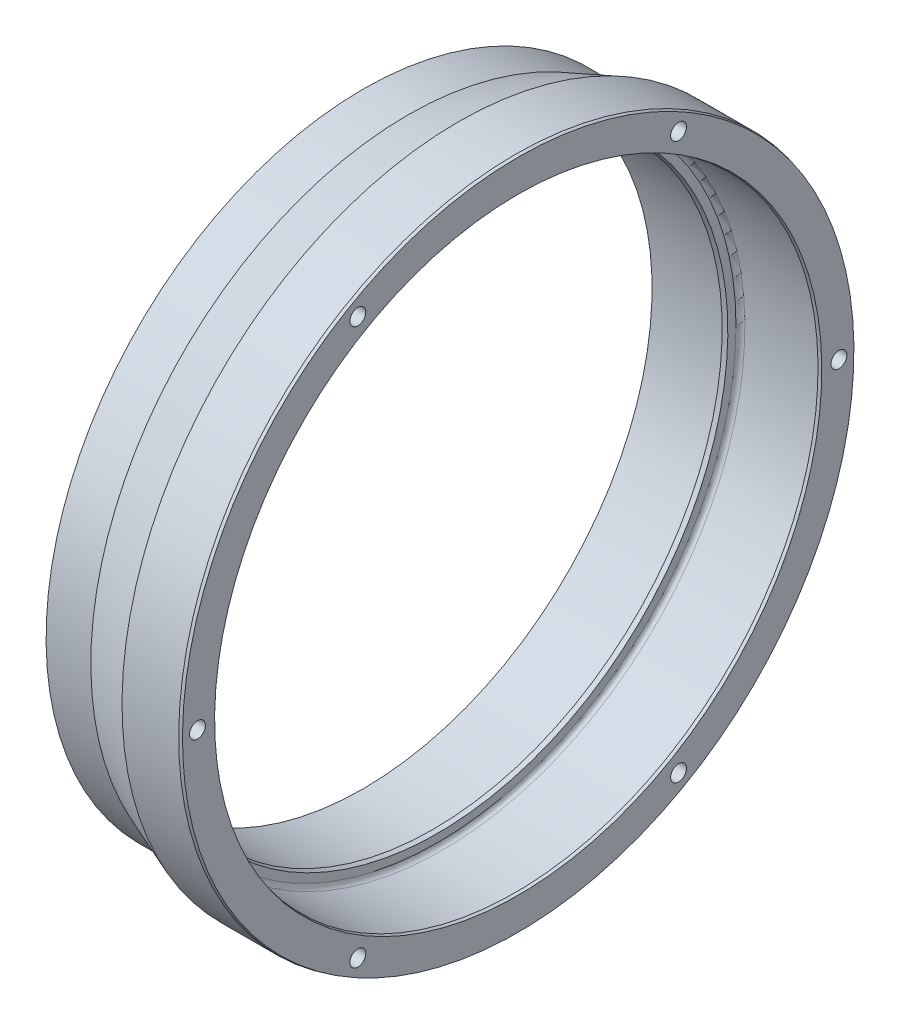
SolidWorks part; units mm, degrees
ref_plane "Front Plane" through (0, 0, 0) normal (0, 0, 1) x (1, 0, 0)
ref_plane "Top Plane" through (0, 0, 0) normal (0, 1, 0) x (1, 0, 0)
ref_plane "Right Plane" through (0, 0, 0) normal (1, 0, 0) x (0, 0, -1)
sketch "Sketch1" plane through (0, 0, 0) normal (0, 0, 1) x (1, 0, 0)
  line L0 (-18.796, 53.975) -> (-10.16, 57.3024)
  line L2 (0, 0) -> (0, 59.8495) construction
  line L3 (-0.508, 57.3024) -> (-10.16, 57.3024)
  line L5 (-18.796, 53.975) -> (-26.416, 53.975)
  line L7 (0, 0) -> (-26.416, 0) construction
  line L8 (-26.416, 53.975) -> (-26.416, 0) construction
  line L9 (-14.478, 49.2125) -> (-13.716, 49.4167)
  line L11 (0, 0) -> (0, 54.3464) construction
  line L12 (-0.508, 51.562) -> (-12.954, 51.562)
  line L13 (-13.716, 49.4167) -> (-13.716, 50.8)
  line L14 (-26.416, 0) -> (0, 0) construction
  line L15 (-26.416, 0) -> (-26.416, 49.2125) construction
  line L16 (-26.416, 49.2125) -> (-14.478, 49.2125)
  line L18 (-0.508, 51.562) -> (0, 51.6981)
  line L19 (-0.508, 57.3024) -> (0, 57.1663)
  line L20 (0, 51.6981) -> (0, 57.1663)
  line L21 (-26.416, 53.975) -> (-26.416, 49.2125)
  arc A0 (-12.954, 51.562) -> (-13.716, 50.8) centre (-12.954, 50.8) ccw
  dimension "D1" = 0.762
  dimension "D2" = 0.508
  dimension "D3" = 15
  dimension "D4" = 0.508
  dimension "D5" = 15
  dimension "D6" = 13.716
  dimension "D7" = 0.762
  dimension "D8" = 15
  dimension "D9" = 10.16
  dimension "D10" = 18.796
  dimension "D11" = 26.416
  dimension "D12" = 53.975
  dimension "D13" = 49.2125
  dimension "D14" = 51.562
  dimension "D15" = 57.3024
revolve "Revolve1" add sketch "Sketch1" angle 360 about L7
hole_wizard "#6-32 Tapped Hole1" positions "Sketch5" profile "Sketch6" tap size "#6-32" standard "ANSI Inch"
sketch "Sketch5" plane through (0, 0, 0) normal (1, 0, 0) x (0, 0, -1)
  point P0 (-54.61, 0)
  dimension "D1" = 54.61
sketch "Sketch6" plane through (0, 0, 54.61) normal (0, 1, 0) x (0, 0, -1)
  line L0 (0, 0) -> (0, 9.7027)
  line L1 (0, 9.7027) -> (1.3525, 8.89)
  line L2 (1.3525, 8.89) -> (1.3525, 0)
  line L5 (1.3525, 0) -> (0, 0)
  line L10 (0, 9.7027) -> (-1.3526, 8.89) construction
  line L11 (0, -6.35) -> (0, 107.95) construction
  dimension "Tap Drill Dia." = 2.7051
  dimension "Tap Drill Depth" = 8.89
  dimension "Drill Angle" = 118
cosmetic thread "Hole Thread1" parameters "D1"=7.112, "D2"=3.5052
pattern_circular "CirPattern1" count 6 over 360 about axis through (0, 0, 0) along (1, 0, 0) of "#6-32 Tapped Hole1"
equation "\"D12@Sketch1\"=4.25/2"
equation "\"D14@Sketch1\"=4.06/2"
equation "\"D1@Sketch5\"=4.3/2"
equation "\"D15@Sketch1\"=4.512/2"
